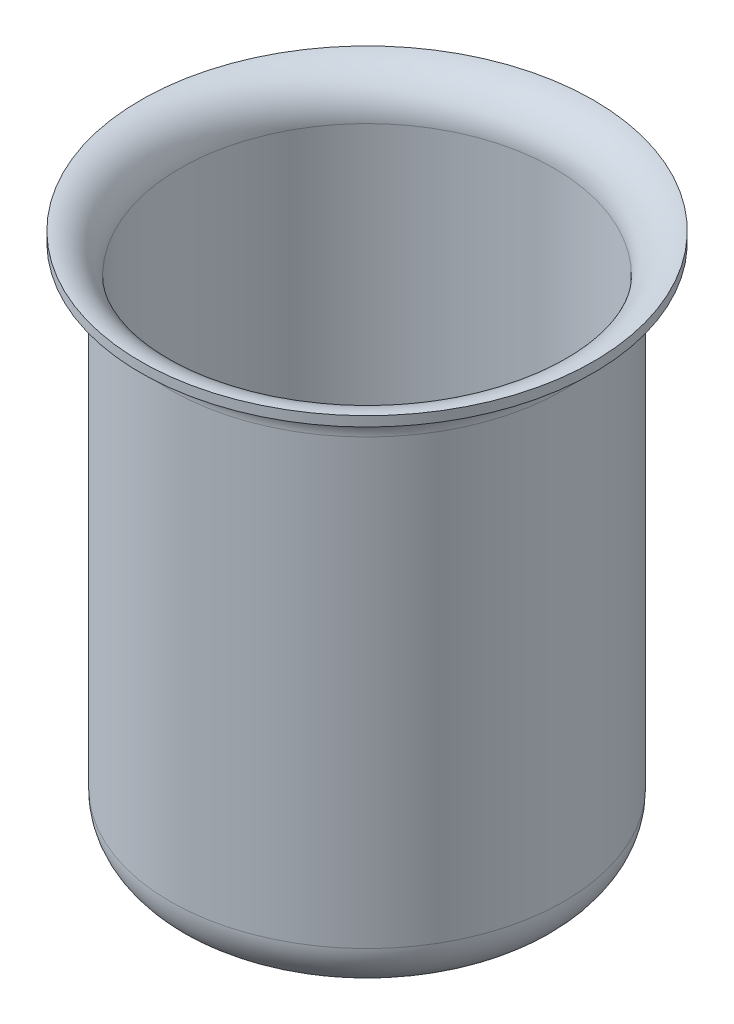
SolidWorks part; units mm, degrees
ref_plane "Přední rovina" through (0, 0, 0) normal (0, 0, 1) x (1, 0, 0)
ref_plane "Horní rovina" through (0, 0, 0) normal (0, 1, 0) x (1, 0, 0)
ref_plane "Pravá rovina" through (0, 0, 0) normal (1, 0, 0) x (0, 0, -1)
sketch "Skica1" plane through (0, 0, 0) normal (0, 0, 1) x (1, 0, 0)
  line L0 (0, 0) -> (-15, 0)
  line L1 (-20, 5) -> (-20, 50)
  line L2 (0, 0) -> (0, 21.0905) construction
  arc A0 (-15, 0) -> (-20, 5) centre (-15, 5) cw
  arc A1 (-20, 50) -> (-23, 53) centre (-23, 50) ccw
  dimension "D3" = 5
  dimension "D4" = 3
  dimension "D1" = 20
  dimension "D2" = 50
  dimension "D5" = 53
revolve "Rotace tenkostěnný1" add sketch "Skica1" angle 360 about L2
